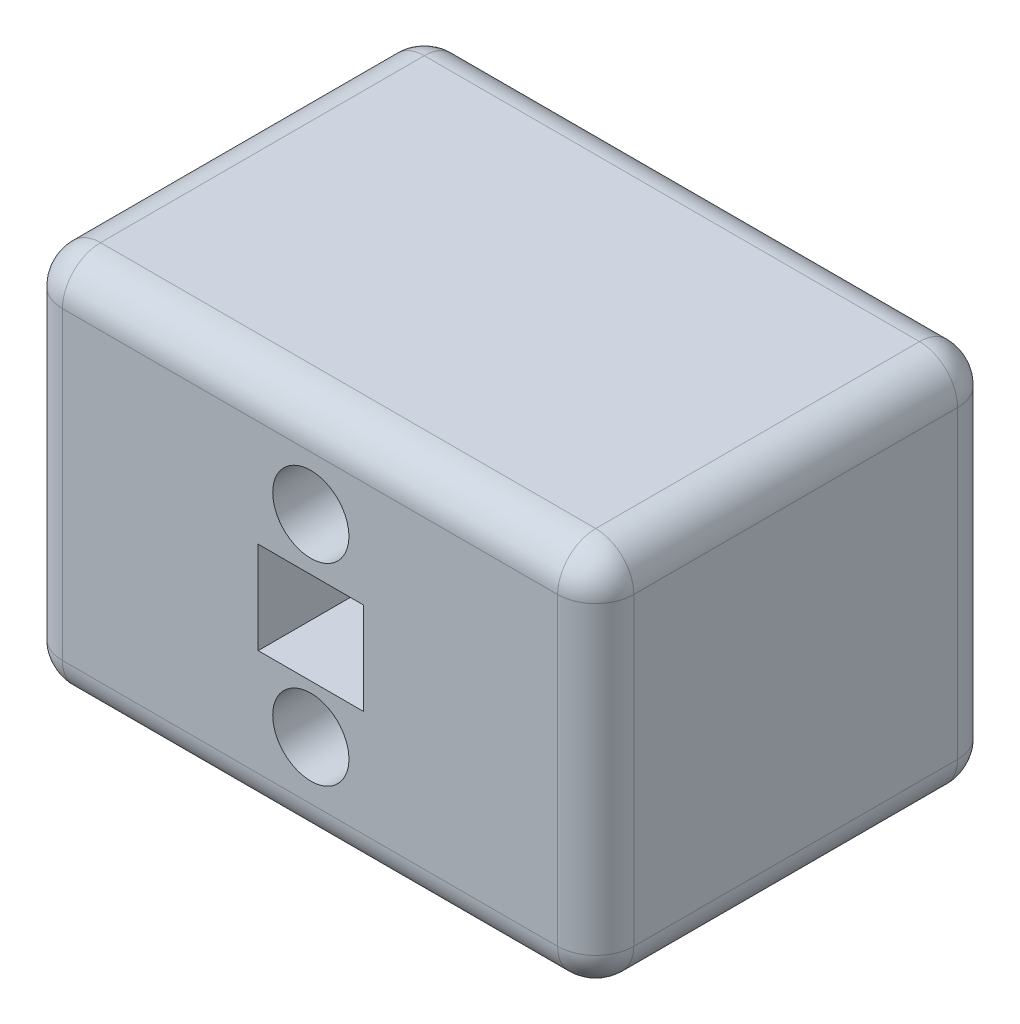
SolidWorks part; units mm, degrees
ref_plane "Front Plane" through (0, 0, 0) normal (0, 0, 1) x (1, 0, 0)
ref_plane "Top Plane" through (0, 0, 0) normal (0, 1, 0) x (1, 0, 0)
ref_plane "Right Plane" through (0, 0, 0) normal (1, 0, 0) x (0, 0, -1)
sketch "Sketch1" plane through (0, 0, 0) normal (0, 0, 1) x (1, 0, 0)
  line L0 (0, 0) -> (0, 100)
  line L1 (0, 100) -> (150, 100)
  line L2 (150, 100) -> (150, 0)
  line L3 (150, 0) -> (0, 0)
  point P4 (0, 0)
  dimension "D1" = 150
  dimension "D2" = 100
extrude "Boss-Extrude1" add sketch "Sketch1" against normal blind 45 and the other way blind 60
sketch "Sketch5" plane through (42.4525, 36, 0) normal (0, 0, 1) x (1, 0, 0)
  line L1 (18.9384, 26.1317) -> (46.5683, 26.1317)
  line L2 (18.9384, 26.1317) -> (18.9384, 1.9288)
  line L3 (18.9384, 1.9288) -> (46.5683, 1.9288)
  line L4 (46.5683, 26.1317) -> (46.5683, 1.9288)
extrude "Cut-Extrude1" cut sketch "Sketch5" against normal blind 83 and the other way blind 79
fillet "Fillet1" radius 10 12 edges at (0, 0, 7.5) (0, 50, -45) (75, 0, -45) (0, 100, 7.5) (75, 100, -45) (150, 100, 7.5) (150, 50, -45) (150, 0, 7.5) (0, 50, 60) (75, 100, 60) (150, 50, 60) (75, 0, 60)
sketch "Sketch7" plane through (0, 0, 0) normal (0, 0, 1) x (1, 0, 0)
  circle A1 centre (75.2059, 75.8191) radius 10
  circle A2 centre (75.2059, 25.174) radius 10
extrude "Cut-Extrude2" cut sketch "Sketch7" against normal mid plane 250
